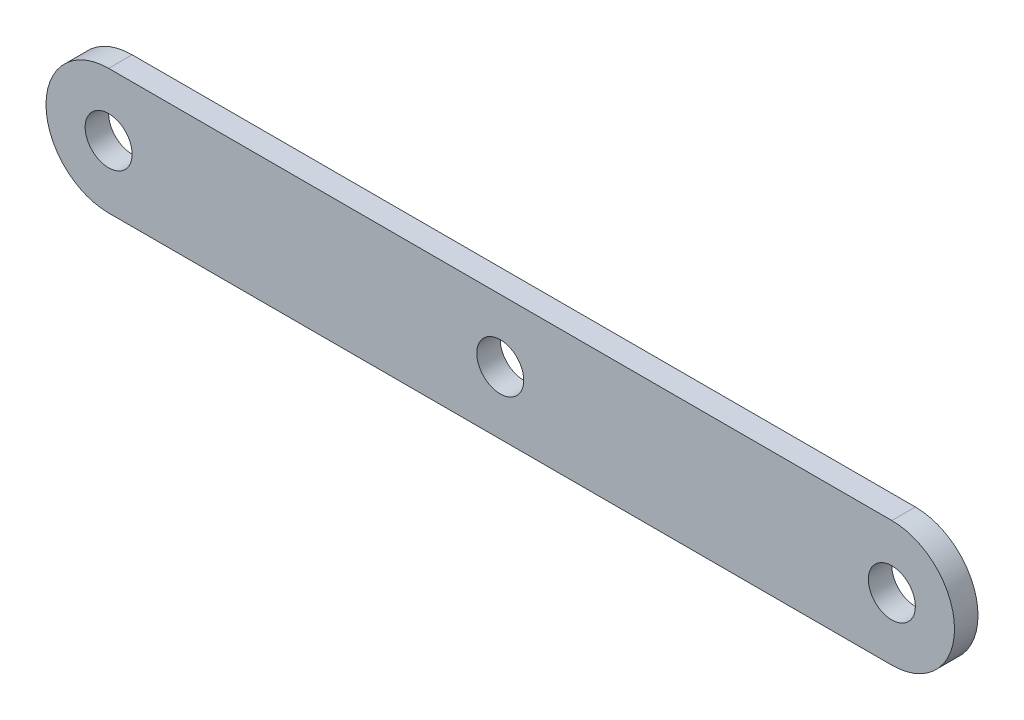
SolidWorks part; units mm, degrees
ref_plane "Front Plane" through (0, 0, 0) normal (0, 0, 1) x (1, 0, 0)
ref_plane "Top Plane" through (0, 0, 0) normal (0, 1, 0) x (1, 0, 0)
ref_plane "Right Plane" through (0, 0, 0) normal (1, 0, 0) x (0, 0, -1)
sketch "Sketch1" plane through (0, 0, 0) normal (0, 0, 1) x (1, 0, 0)
  line L0 (-50, 0) -> (50, 0) construction
  line L1 (-50, 8) -> (50, 8)
  line L2 (-50, -8) -> (50, -8)
  arc A0 (-50, 8) -> (-50, -8) centre (-50, 0) ccw
  arc A1 (50, -8) -> (50, 8) centre (50, 0) ccw
  circle A2 centre (-50, 0) radius 3
  circle A3 centre (50, 0) radius 3
  circle A4 centre (0, 0) radius 3
  point P3 (0, 0)
  dimension "D1" = 6
  dimension "D2" = 8
  dimension "D3" = 100
extrude "Boss-Extrude1" add sketch "Sketch1" along normal blind 3
